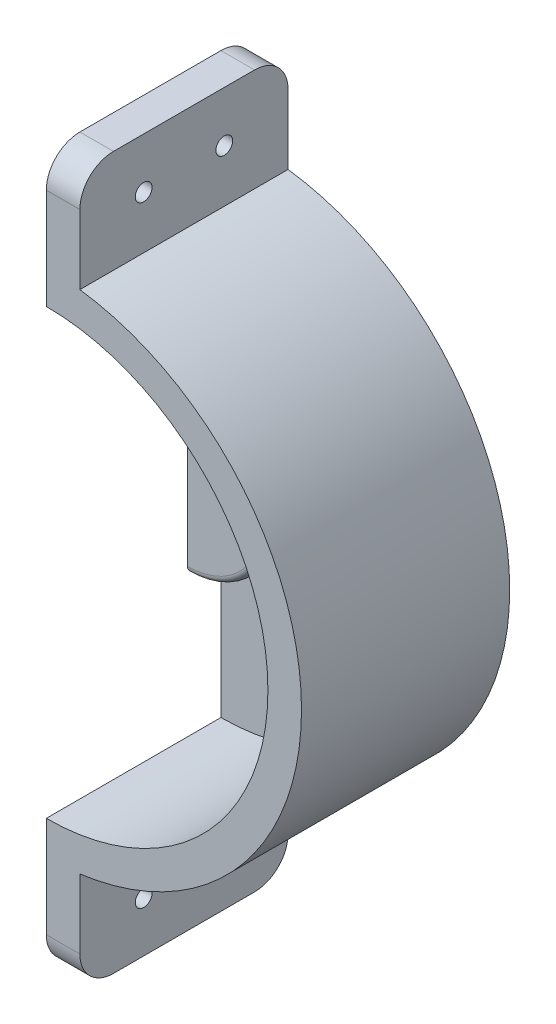
SolidWorks part; units mm, degrees
ref_plane "Alzado" through (0, 0, 0) normal (0, 0, 1) x (1, 0, 0)
ref_plane "Planta" through (0, 0, 0) normal (0, 1, 0) x (1, 0, 0)
ref_plane "Vista lateral" through (0, 0, 0) normal (1, 0, 0) x (0, 0, -1)
sketch "Croquis1" plane through (0, 0, 0) normal (0, 0, 1) x (1, 0, 0)
  line L0 (0, -38) -> (0, 38)
  line L1 (0, 38) -> (0, 53)
  line L2 (0, 53) -> (5, 53)
  line L3 (5, 53) -> (5, 37.6696)
  line L4 (0, -38) -> (0, -53)
  line L5 (0, -53) -> (5, -53)
  line L6 (5, -53) -> (5, -37.6696)
  arc A2 (5, -37.6696) -> (5, 37.6696) centre (0, 0) ccw
  point P7 (0, 0)
extrude "Saliente-Extruir1" add sketch "Croquis1" along normal blind 5
sketch "Croquis2" plane through (0, 0, 5) normal (0, 0, 1) x (1, 0, 0)
  line L0 (0, -38) -> (0, -33)
  line L2 (0, 33) -> (0, 38)
  arc A0 (0, -33) -> (0, 33) centre (0, 0) ccw
  arc A1 (0, -38) -> (0, 38) centre (0, 0) ccw
extrude "Saliente-Extruir2" add sketch "Croquis2" along normal blind 26
sketch "Croquis3" plane through (0, 0, 5) normal (0, 0, 1) x (1, 0, 0)
  line L0 (0, 33) -> (0, -33) construction
  line L1 (0, 12) -> (0, -12)
  arc A0 (0, -12) -> (0, 12) centre (0, 0) ccw
extrude "Saliente-Extruir3" add sketch "Croquis3" along normal blind 5
fillet "Redondeo1" radius 1 1 edges at (12, 0, 10)
sketch "Croquis4" plane through (0, 0, 5) normal (0, 0, 1) x (1, 0, 0)
  line L3 (0, -38) -> (0, -53)
  line L4 (0, -53) -> (5, -53)
  line L5 (5, -53) -> (5, -37.6696)
  line L6 (0, -38) -> (0, -53)
  line L7 (0, -53) -> (5, -53)
  line L8 (5, -53) -> (5, -37.6696)
  line L9 (5, 37.6696) -> (5, 53)
  line L10 (5, 53) -> (0, 53)
  line L11 (0, 53) -> (0, 38)
  line L12 (5, 37.6696) -> (5, 53)
  line L13 (5, 53) -> (0, 53)
  line L14 (0, 53) -> (0, 38)
  arc A1 (0, -38) -> (5, -37.6696) centre (0, 0) ccw
  arc A2 (0, -38) -> (5, -37.6696) centre (0, 0) ccw
  arc A3 (5, 37.6696) -> (0, 38) centre (0, 0) ccw
  arc A4 (5, 37.6696) -> (0, 38) centre (0, 0) ccw
  dimension "D1" = 0
  dimension "D2" = 0
extrude "Saliente-Extruir4" add sketch "Croquis4" along normal up to surface (26 mm away) up to face at (17.75, 0, 31)
fillet "Redondeo2" radius 5 4 edges at (2.5, -53, 0) (2.5, -53, 31) (2.5, 53, 0) (2.5, 53, 31)
sketch "Croquis5" plane through (0, 0, 0) normal (-1, 0, 0) x (0, 0, 1)
  line L0 (0, 0) -> (29.6586, 0) construction
  line L1 (15.5, 53) -> (15.5, 45.5) construction
  line L2 (26, 53) -> (5, 53) construction
  line L3 (9.5, 45.5) -> (21.5, 45.5) construction
  circle A0 centre (9.5, 45.5) radius 1.25
  circle A1 centre (21.5, 45.5) radius 1.25
  circle A2 centre (21.5, -45.5) radius 1.25
  circle A3 centre (9.5, -45.5) radius 1.25
  point P10 (15.5, 45.5)
extrude "Cortar-Extruir1" cut sketch "Croquis5" against normal blind 5
